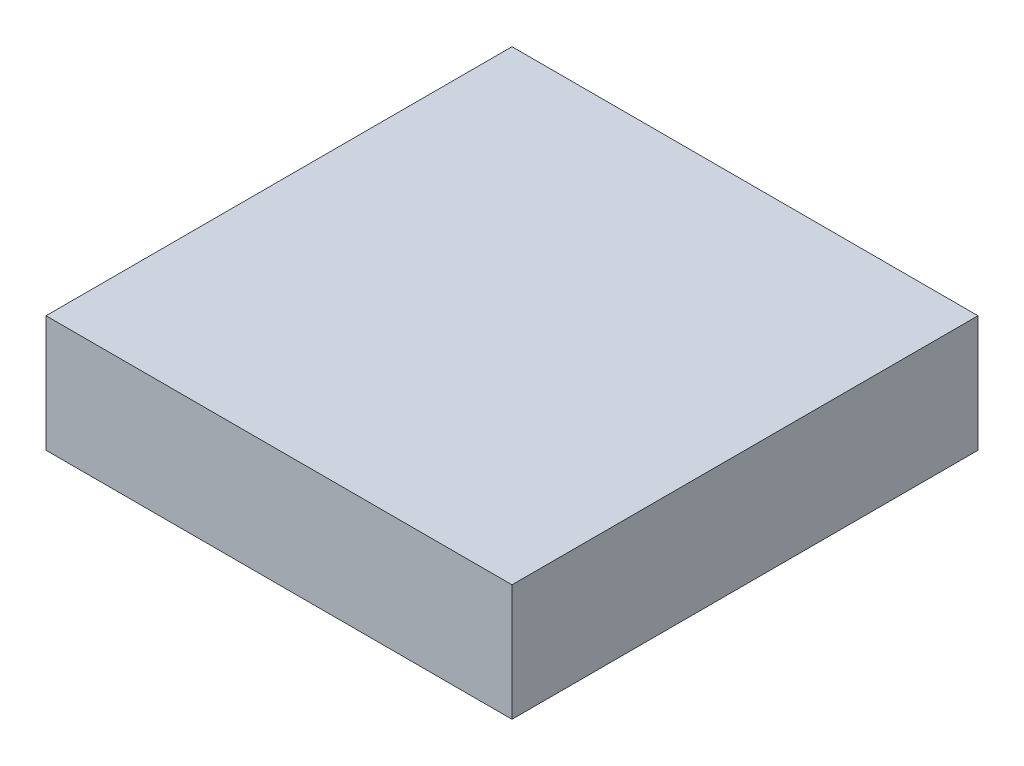
SolidWorks part; units mm, degrees
ref_plane "Front Plane" through (0, 0, 0) normal (0, 0, 1) x (1, 0, 0)
ref_plane "Top Plane" through (0, 0, 0) normal (0, 1, 0) x (1, 0, 0)
ref_plane "Right Plane" through (0, 0, 0) normal (1, 0, 0) x (0, 0, -1)
sketch "Sketch1" plane through (0, 0, 0) normal (0, 1, 0) x (1, 0, 0)
  line L1 (-12.7, -12.7) -> (12.7, -12.7)
  line L2 (-12.7, -12.7) -> (-12.7, 12.7)
  line L3 (-12.7, 12.7) -> (12.7, 12.7)
  line L4 (12.7, -12.7) -> (12.7, 12.7)
  line L5 (-12.7, -12.7) -> (12.7, 12.7) construction
  line L6 (-12.7, 12.7) -> (12.7, -12.7) construction
  point P0 (0, 0)
  dimension "D1" = 25.4
  dimension "D2" = 25.4
extrude "Boss-Extrude1" add sketch "Sketch1" along normal blind 6.35
